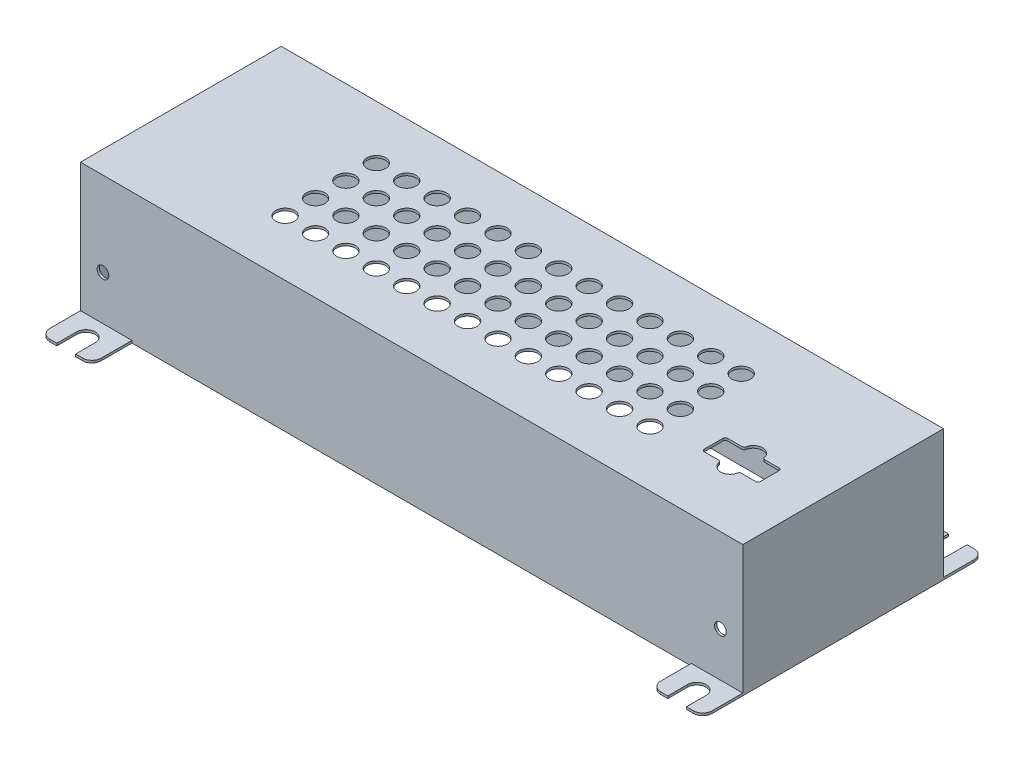
SolidWorks part; units mm, degrees
material "Lega 1060"
ref_plane "Piano frontale" through (0, 0, 0) normal (0, 0, 1) x (1, 0, 0)
ref_plane "Piano superiore" through (0, 0, 0) normal (0, 1, 0) x (1, 0, 0)
ref_plane "Piano destro" through (0, 0, 0) normal (1, 0, 0) x (0, 0, -1)
sketch "Schizzo1" plane through (0, 0, 0) normal (0, 1, 0) x (1, 0, 0)
  line L1 (-70.8, -21.45) -> (70.8, -21.45)
  line L2 (-70.8, -21.45) -> (-70.8, 21.45)
  line L3 (-70.8, 21.45) -> (70.8, 21.45)
  line L4 (70.8, -21.45) -> (70.8, 21.45)
  line L5 (-70.8, -21.45) -> (70.8, 21.45) construction
  line L6 (-70.8, 21.45) -> (70.8, -21.45) construction
  point P0 (0, 0)
  dimension "D1" = 141.6
  dimension "D2" = 42.9
extrude "Estrusione-Estrusione1" add sketch "Schizzo1" along normal blind 28
shell "Svuota1" thickness 0.5
hole_wizard "Foro Ø4.0 (4)-1" positions "Schizzo3" profile "Schizzo2" hole size "Ø4.0" standard "Ansi Metric"
sketch "Schizzo3" plane through (0, 28, 0) normal (0, 1, 0) x (1, 0, 0)
  line L0 (-39, 10) -> (0, 10) construction
  line L1 (0, 10) -> (0, 0) construction
  point P0 (-39, 10)
  dimension "D1" = 39
  dimension "D2" = 10
sketch "Schizzo2" plane through (-39, 28, -10) normal (1, 0, 0) x (0, 0, 1)
  line L0 (0, 0) -> (0, 7.2017)
  line L1 (0, 7.2017) -> (2, 6)
  line L2 (2, 6) -> (2, 0)
  line L5 (2, 0) -> (0, 0)
  line L10 (0, 7.2017) -> (-2, 6) construction
  line L11 (0, -6.35) -> (0, 107.95) construction
  dimension "Hole Dia." = 4
  dimension "Hole Depth" = 6
  dimension "Drill Angle" = 118
pattern_linear "Ripetizione a L1" count 13 spacing 6.5 along (1, 0, 0) count 4 spacing 6.5 along (0, 0, 1) of "Foro Ø4.0 (4)-1"
sketch "Schizzo4" plane through (0, 28, 0) normal (0, 1, 0) x (1, 0, 0)
  line L0 (0, 0) -> (55, 0) construction
  line L1 (49, -8.4) -> (61, -8.4)
  line L2 (49, -8.4) -> (49, -3.4)
  line L3 (49, -3.4) -> (61, -3.4)
  line L4 (61, -8.4) -> (61, -3.4)
  line L5 (49, -8.4) -> (61, -3.4) construction
  line L6 (49, -3.4) -> (61, -8.4) construction
  line L7 (55, 0) -> (55, -5.9) construction
  point P0 (55, -5.9)
  dimension "D1" = 12
  dimension "D2" = 5
  dimension "D3" = 5.9
  dimension "D4" = 55
extrude "Taglio-Estrusione1" cut sketch "Schizzo4" against normal blind 28
sketch "Schizzo6" plane through (0, 28, 0) normal (0, 1, 0) x (1, 0, 0)
  line L0 (61, -3.4) -> (49, -3.4) construction
  line L2 (49, -8.4) -> (61, -8.4) construction
  line L3 (53, -3.4) -> (57, -3.4)
  line L4 (57, -8.4) -> (53, -8.4)
  arc A0 (57, -3.4) -> (53, -3.4) centre (55, -3.4) ccw
  arc A1 (53, -8.4) -> (57, -8.4) centre (55, -8.4) ccw
  dimension "D1" = 2
extrude "Taglio-Estrusione2" cut sketch "Schizzo6" against normal blind 28
sketch "Schizzo8" plane through (0, 0, 0) normal (0, 1, 0) x (1, 0, 0)
  line L1 (-70.8, 21.45) -> (-59.8, 21.45)
  line L2 (-70.8, 21.45) -> (-70.8, 30)
  line L3 (-70.8, 30) -> (-59.8, 30)
  line L4 (-59.8, 21.45) -> (-59.8, 30)
  line L5 (-70.8, -21.45) -> (-59.8, -21.45)
  line L6 (-70.8, -21.45) -> (-70.8, -30)
  line L7 (-70.8, -30) -> (-59.8, -30)
  line L8 (-59.8, -21.45) -> (-59.8, -30)
  dimension "D1" = 60
  dimension "D2" = 11
extrude "Estrusione-Estrusione2" add sketch "Schizzo8" along normal blind 0.5
sketch "Schizzo9" plane through (0, 0.5, 0) normal (0, 1, 0) x (1, 0, 0)
  line L0 (-59.8, 30) -> (-70.8, 30) construction
  line L1 (-67.3, 30) -> (-63.3, 30)
  line L2 (-67.3, 30) -> (-67.3, 25.8)
  line L3 (-67.3, 25.8) -> (-63.3, 25.8) construction
  line L4 (-63.3, 30) -> (-63.3, 25.8)
  line L5 (-70.8, -30) -> (-59.8, -30) construction
  line L6 (-67.3, -30) -> (-63.3, -30)
  line L7 (-67.3, -30) -> (-67.3, -25.8)
  line L8 (-67.3, -25.8) -> (-63.3, -25.8) construction
  line L9 (-63.3, -30) -> (-63.3, -25.8)
  line L10 (-65.3, -23.8) -> (-63.3, -23.8) construction
  line L11 (-63.3, -23.8) -> (-63.3, -25.8) construction
  line L12 (-67.3, -27.9) -> (-70.8, -27.9) construction
  line L13 (-70.8, -21.45) -> (-70.8, -30) construction
  line L14 (-63.3, -27.9) -> (-59.8, -27.9) construction
  line L15 (-59.8, -30) -> (-59.8, -21.45) construction
  arc A0 (-63.3, 25.8) -> (-67.3, 25.8) centre (-65.3, 25.8) cw
  arc A1 (-63.3, -25.8) -> (-67.3, -25.8) centre (-65.3, -25.8) ccw
  dimension "D1" = 51.6
  dimension "D2" = 2
  dimension "D3" = 6.2
extrude "Taglio-Estrusione3" cut sketch "Schizzo9" against normal blind 10
pattern_linear "Ripetizione a L2" count 2 spacing 130.6 along (1, 0, 0) of "Estrusione-Estrusione2", "Taglio-Estrusione3"
hole_wizard "Foro filettato M3x0.5-1" positions "Schizzo11" profile "Schizzo10" tap size "M3x0.5" standard "Ansi Metric" end condition through all
sketch "Schizzo11" plane through (0, 0, 21.45) normal (0, 0, 1) x (1, 0, 0)
  line L0 (-66, 10) -> (0, 10) construction
  line L1 (0, 10) -> (66, 10) construction
  line L2 (66, 10) -> (70.8, 10) construction
  line L3 (70.8, 28) -> (70.8, 0.5) construction
  line L5 (-66, 10) -> (-70.8, 10) construction
  line L6 (-70.8, 28) -> (-70.8, 0.5) construction
  line L8 (0, 10) -> (0, 0) construction
  line L9 (-59.8, 0) -> (59.8, 0) construction
  point P0 (-66, 10)
  point P2 (66, 10)
  dimension "D1" = 10
  dimension "D2" = 132
cosmetic thread "Filettatura del foro1" parameters "D2"=3
cosmetic thread "Filettatura del foro2" parameters "D2"=3
sketch "Schizzo10" plane through (-66, 10, 21.45) normal (1, 0, 0) x (0, -1, 0)
  line L0 (0, 0) -> (0, 51.45)
  line L1 (0, 51.45) -> (1.25, 51.45)
  line L2 (1.25, 51.45) -> (1.25, 0)
  line L5 (1.25, 0) -> (0, 0)
  line L11 (0, -6.35) -> (0, 107.95) construction
  dimension "Thru Tap Drill Dia." = 2.5
  dimension "Thru Tap Drill Depth" = 51.45
fillet "Raccordo2" radius 2 8 edges at (-59.8, 0.25, -30) (-70.8, 0.25, -30) (-70.8, 0.25, 30) (-59.8, 0.25, 30) (59.8, 0.25, -30) (70.8, 0.25, -30) (59.8, 0.25, 30) (70.8, 0.25, 30)
fillet "Raccordo3" radius 0.5 8 edges at (49, 27.75, 3.4) (49, 27.75, 8.4) (61, 27.75, 3.4) (61, 27.75, 8.4) (57, 27.75, 3.4) (53, 27.75, 3.4) (53, 27.75, 8.4) (57, 27.75, 8.4)
